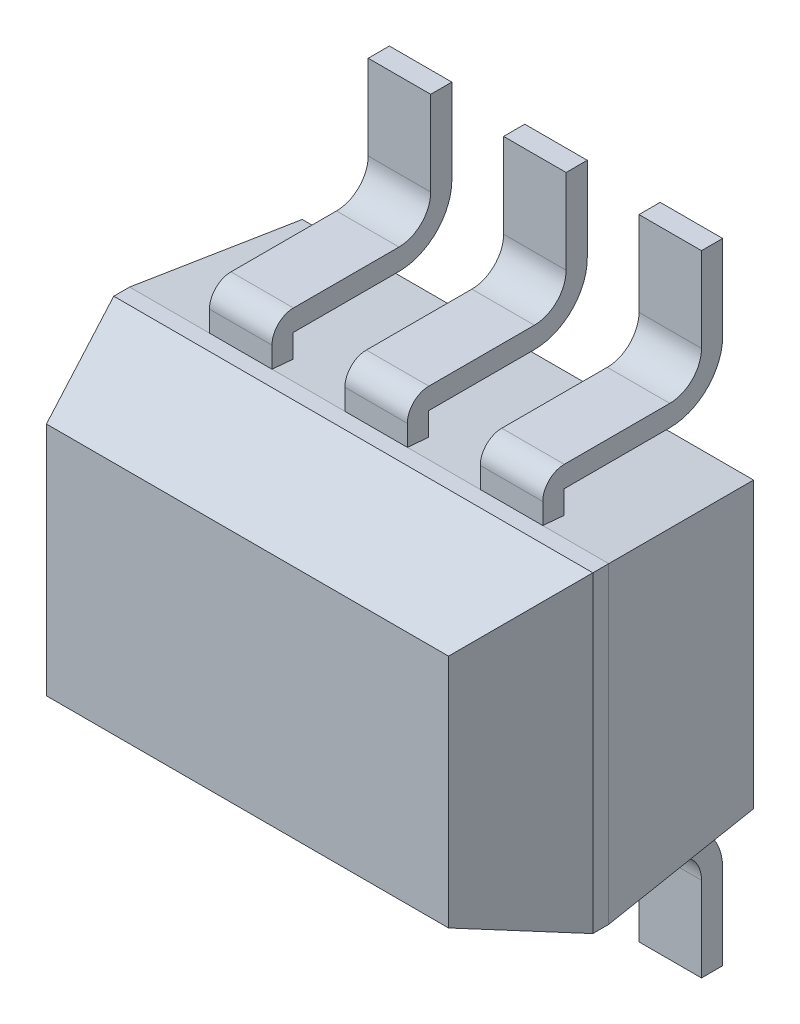
SolidWorks part; units mm, degrees
ref_plane "x/y" through (0, 0, 0) normal (0, 0, 1) x (1, 0, 0)
ref_plane "x/z" through (0, 0, 0) normal (0, 1, 0) x (1, 0, 0)
ref_plane "y/z" through (0, 0, 0) normal (1, 0, 0) x (0, 0, -1)
sketch "Sketch1" plane through (0, 0, 0) normal (0, 0, 1) x (1, 0, 0)
  line L0 (2.0505, 2.262) -> (4.3505, 2.262)
  line L1 (2.0505, 2.262) -> (2.0505, 0.762)
  line L2 (4.3505, 0.762) -> (2.0505, 0.762)
  line L3 (4.3505, 0.762) -> (4.3505, 2.262)
  dimension "D1" = 1.5
  dimension "D2" = 2.3
extrude "Base-Extrude" add sketch "Sketch1" along normal blind 1.3462
ref_plane "Plane1" through (2.0505, 0, 0) normal (1, 0, 0) x (0, 0, -1)
ref_plane "Plane2" through (0, 2.262, 0) normal (0, 1, 0) x (-1, 0, 0)
ref_plane "Plane3" through (4.3505, 0, 0) normal (1, 0, 0) x (0, 0, -1)
ref_plane "Plane4" through (0, 0.762, 0) normal (0, 1, 0) x (-1, 0, 0)
chamfer "Chamfer1" distance 0.508 angle 20 4 edges at (2.0505, 1.512, 1.3462) (3.2005, 2.262, 1.3462) (4.3505, 1.512, 1.3462) (3.2005, 0.762, 1.3462)
chamfer "Chamfer2" distance 0.762 angle 5 4 edges at (3.2005, 0.762, 0) (4.3505, 1.512, 0) (3.2005, 2.262, 0) (2.0505, 1.512, 0)
sketch "Sketch3" plane through (0.1189, 0.143, 1.3462) normal (0, 0, 1) x (1, 0, 0)
  line L0 (4.0467, 0.8039) -> (4.0467, 1.9341) construction
  circle A0 centre (1.9467, 1.27) radius 0.15
  dimension "D2" = 0.3
  dimension "D1" = 2.1
extrude "Cut-Extrude1" cut sketch "Sketch3" against normal blind 0.127
ref_plane "Plane5" through (2.5839, 0, 0) normal (1, 0, 0) x (0, 0, -1)
sketch "Sketch4" plane through (2.5839, 0, 0) normal (1, 0, 0) x (0, 0, -1)
  line L0 (-0.762, 0.662) -> (-0.762, 1.062)
  line L1 (0, 0.4064) -> (0, 0)
  line L2 (-0.6588, 0.5588) -> (-0.1524, 0.5588)
  line L5 (-0.762, 2.262) -> (-0.762, 0.762) construction
  arc A0 (-0.762, 0.662) -> (-0.6588, 0.5588) centre (-0.6588, 0.662) ccw
  arc A1 (-0.1524, 0.5588) -> (0, 0.4064) centre (-0.1524, 0.4064) cw
extrude "Boss-Extrude-Thin3" add sketch "Sketch4" along normal mid plane 0.3 thin
pattern_linear "LPattern1" count 3 spacing 0.65 along (1, 0, 0) of "Boss-Extrude-Thin3"
ref_plane "Plane6" through (0, 1.512, 0) normal (0, 1, 0) x (-1, 0, 0)
mirror "Mirror1" about plane through (0, 1.512, 0) normal (0, 1, 0) of "Boss-Extrude-Thin3", "LPattern1"
